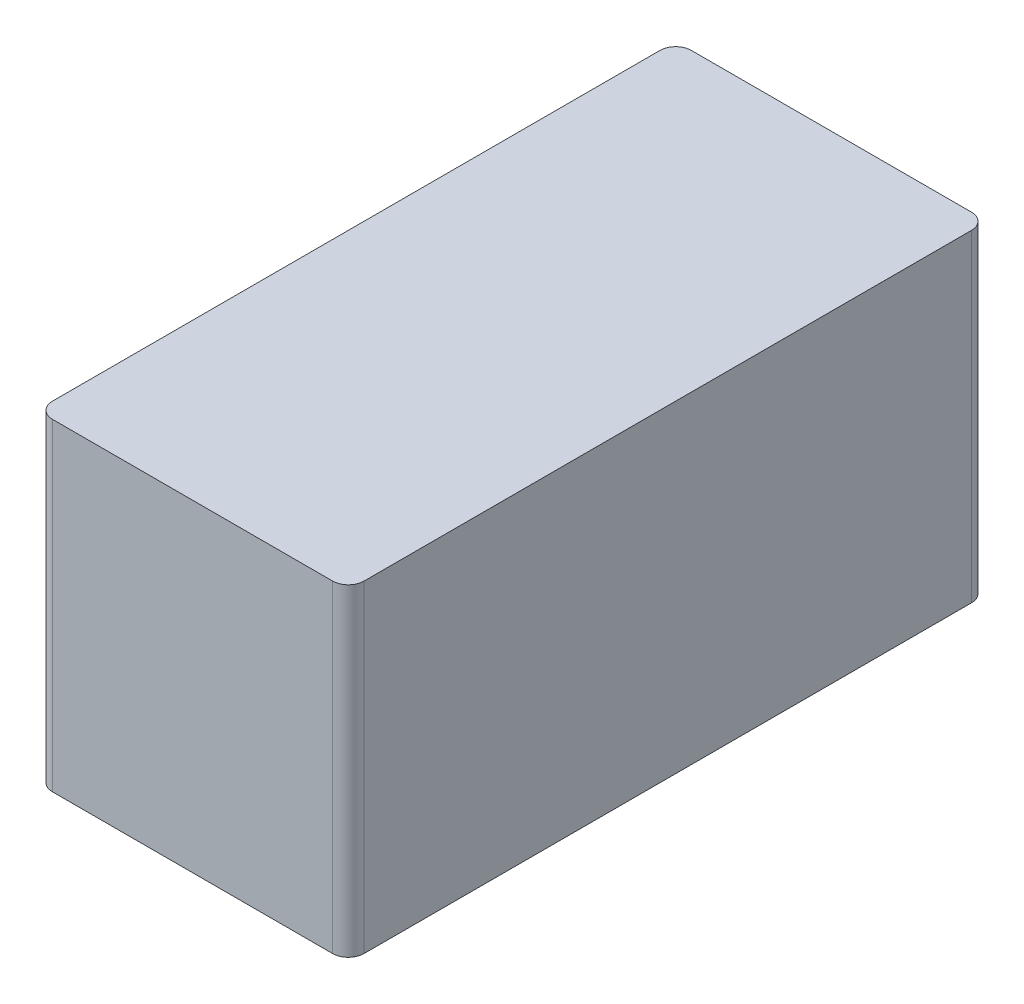
SolidWorks part; units mm, degrees
material "Polyethylene Cross-Linked"
ref_plane "Front Plane" through (0, 0, 0) normal (0, 0, 1) x (1, 0, 0)
ref_plane "Top Plane" through (0, 0, 0) normal (0, 1, 0) x (1, 0, 0)
ref_plane "Right Plane" through (0, 0, 0) normal (1, 0, 0) x (0, 0, -1)
sketch "Sketch1" plane through (0, 0, 0) normal (0, 1, 0) x (1, 0, 0)
  line L1 (-9.9, 20.3) -> (9.9, 20.3)
  line L2 (-9.9, 20.3) -> (-9.9, -20.3)
  line L3 (-9.9, -20.3) -> (9.9, -20.3)
  line L4 (9.9, 20.3) -> (9.9, -20.3)
  line L5 (-9.9, 20.3) -> (9.9, -20.3) construction
  line L6 (-9.9, -20.3) -> (9.9, 20.3) construction
  point P0 (0, 0)
  dimension "D1" = 19.8
  dimension "D2" = 40.6
extrude "Boss-Extrude1" add sketch "Sketch1" along normal mid plane 20.5
fillet "Fillet1" radius 1 4 edges at (-9.9, 0, -20.3) (9.9, 0, -20.3) (9.9, 0, 20.3) (-9.9, 0, 20.3)
